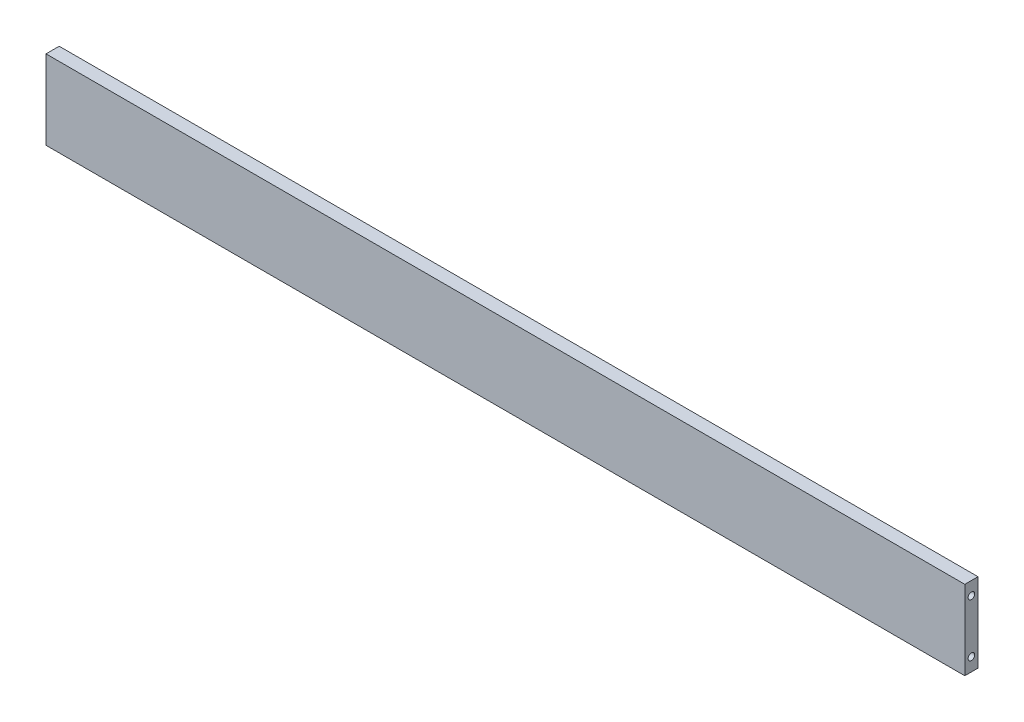
SolidWorks part; units mm, degrees
material "A3钢"
ref_plane "前视基准面" through (0, 0, 0) normal (0, 0, 1) x (1, 0, 0)
ref_plane "上视基准面" through (0, 0, 0) normal (0, 1, 0) x (1, 0, 0)
ref_plane "右视基准面" through (0, 0, 0) normal (1, 0, 0) x (0, 0, -1)
sketch "草图1" plane through (0, 0, 0) normal (0, 0, 1) x (1, 0, 0)
  line L1 (-348, -30) -> (348, -30)
  line L2 (-348, -30) -> (-348, 30)
  line L3 (-348, 30) -> (348, 30)
  line L4 (348, -30) -> (348, 30)
  line L5 (-348, -30) -> (348, 30) construction
  line L6 (-348, 30) -> (348, -30) construction
  point P0 (0, 0)
  dimension "D1" = 696
  dimension "D2" = 60
extrude "凸台-拉伸1" add sketch "草图1" along normal mid plane 10
sketch "草图8" plane through (0, 0, -5) normal (0, 0, -1) x (-1, 0, 0)
  line L0 (-340.5, 63.1507) -> (-340.5, -55.892) construction
  line L1 (-348, -30) -> (-348, 30) construction
  line L2 (-348, 30) -> (348, 30) construction
  circle A0 centre (-340.5, 20) radius 2.5
  circle A1 centre (-340.5, -30) radius 2.5
  circle A2 centre (-340.5, -80) radius 2.5
  dimension "D1" = 5
  dimension "D3" = 10
  dimension "D4" = 100
  dimension "D5" = 50
  dimension "D2" = 7.5
ref_plane "基准面1" through (0, 0, 0) normal (1, 0, 0) x (0, 0, -1)
sketch "草图10" plane through (348, 0, 0) normal (1, 0, 0) x (0, 0, -1)
  line L0 (0, 30) -> (0, 20) construction
  line L1 (-5, 30) -> (5, 30) construction
  dimension "D1" = 10
hole_wizard "M6 螺纹孔2" positions "3D草图2" profile "草图11" tap size "M6" standard "GB"
sketch3d "3D草图2"
  point P0 (348, 20, 0)
sketch "草图11" plane through (348, 20, 0) normal (0, 1, 0) x (0, 0, -1)
  line L0 (0, 0) -> (0, 16.5022)
  line L1 (0, 16.5022) -> (2.5, 15)
  line L2 (2.5, 15) -> (2.5, 0)
  line L5 (2.5, 0) -> (0, 0)
  line L10 (0, 16.5022) -> (-2.5, 15) construction
  line L11 (0, -6.35) -> (0, 107.95) construction
  dimension "螺纹孔钻头直径" = 5
  dimension "螺纹孔钻头深度" = 15
  dimension "导头角度" = 118
cosmetic thread "孔螺蚊线2" parameters "D1"=12, "D2"=6
pattern_linear "阵列(线性)1" count 2 spacing 40 along (0, -1, 0) of "M6 螺纹孔2"
ref_plane "基准面2" through (0, 0, 0) normal (1, 0, 0) x (0, 0, -1)
mirror "镜向2" about plane through (0, 0, 0) normal (1, 0, 0) of "阵列(线性)1", "M6 螺纹孔2"
sketch "草图12" plane through (0, -30, 0) normal (0, -1, 0) x (1, 0, 0)
  line L0 (0, 53.9225) -> (0, -86.1066) construction
  line L1 (-150, 0) -> (150, 0) construction
  line L2 (150, 0) -> (300, 0) construction
  line L4 (-150, 0) -> (-300, 0) construction
  dimension "D1" = 300
  dimension "D2" = 150
hole_wizard "M6 螺纹孔1" positions "3D草图3" profile "草图13" tap size "M6" standard "GB"
sketch3d "3D草图3"
  line L1 (0, -30, 53.9225) -> (0, -30, -86.1066) construction
  line L2 (-150, -30, 0) -> (150, -30, 0) construction
  point P0 (-300, -30, 0)
  point P3 (-150, -30, 0)
  point P6 (150, -30, 0)
  point P9 (300, -30, 0)
  point P16 (0, -30, 0)
sketch "草图13" plane through (-300, -30, 0) normal (1, 0, 0) x (0, 0, -1)
  line L0 (0, 0) -> (0, 16.5022)
  line L1 (0, 16.5022) -> (2.5, 15)
  line L2 (2.5, 15) -> (2.5, 0)
  line L5 (2.5, 0) -> (0, 0)
  line L10 (0, 16.5022) -> (-2.5, 15) construction
  line L11 (0, -6.35) -> (0, 107.95) construction
  dimension "螺纹孔钻头直径" = 5
  dimension "螺纹孔钻头深度" = 15
  dimension "导头角度" = 118
cosmetic thread "孔螺蚊线3" parameters "D1"=12, "D2"=6
cosmetic thread "孔螺蚊线4" parameters "D1"=12, "D2"=6
cosmetic thread "孔螺蚊线5" parameters "D1"=12, "D2"=6
cosmetic thread "孔螺蚊线6" parameters "D1"=12, "D2"=6
cosmetic thread "孔螺蚊线7" parameters "D1"=12, "D2"=6
